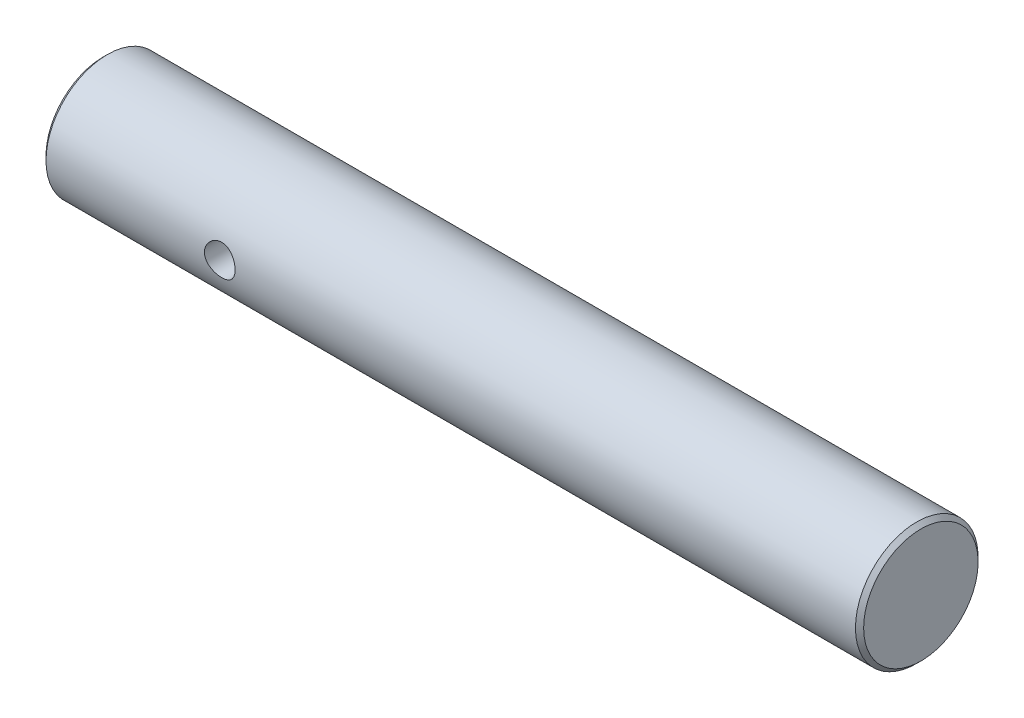
SolidWorks part; units mm, degrees
ref_plane "Plan de face" through (0, 0, 0) normal (0, 0, 1) x (1, 0, 0)
ref_plane "Plan de dessus" through (0, 0, 0) normal (0, 1, 0) x (1, 0, 0)
ref_plane "Plan de droite" through (0, 0, 0) normal (1, 0, 0) x (0, 0, -1)
sketch "Esquisse1" plane through (0, 0, 0) normal (0, 0, 1) x (1, 0, 0)
  line L1 (-15, 3) -> (25, 3)
  line L2 (-15, 3) -> (-15, 0)
  line L3 (-15, 0) -> (25, 0)
  line L4 (25, 3) -> (25, 0)
  dimension "D1" = 40
  dimension "D2" = 3
revolve "Révolution1" add sketch "Esquisse1" angle 360 about L3
chamfer "Chanfrein1" distance 0.2 angle 45 2 edges at (25, 0, 3) (-15, 0, 3)
sketch "Esquisse2" plane through (0, 0, 0) normal (0, 0, 1) x (1, 0, 0)
  line L0 (-15, 2.8) -> (-15, -2.8) construction
  circle A0 centre (-6.3, 0) radius 0.75
  dimension "D1" = 1.5
  dimension "D2" = 8.7
extrude "Enlèv. mat.-Extru.1" cut sketch "Esquisse2" against normal through all and the other way through all
